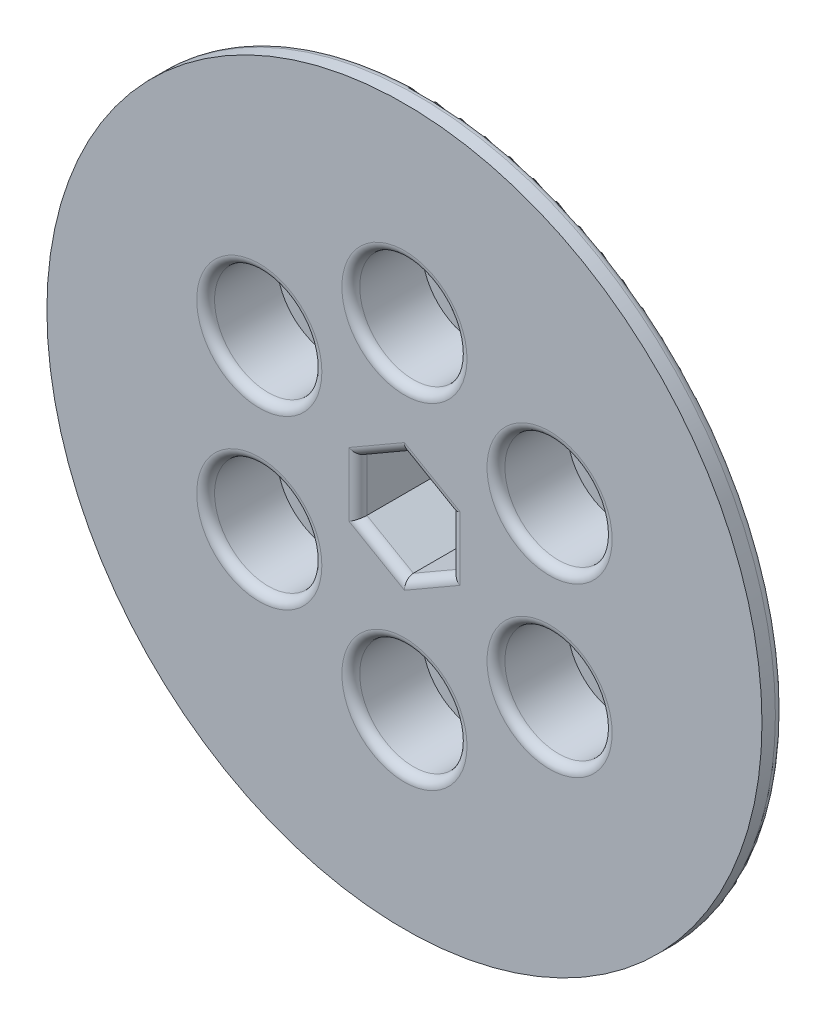
SolidWorks part; units mm, degrees
ref_plane "Front" through (0, 0, 0) normal (0, 0, 1) x (1, 0, 0)
ref_plane "Top" through (0, 0, 0) normal (0, 1, 0) x (1, 0, 0)
ref_plane "Right" through (0, 0, 0) normal (1, 0, 0) x (0, 0, -1)
sketch "Sketch1" plane through (0, 0, 0) normal (0, 0, 1) x (1, 0, 0)
  circle A0 centre (0, 0) radius 31.75
  dimension "D1" = 63.5
extrude "Boss-Extrude1" add sketch "Sketch1" along normal blind 12.7
sketch "Sketch2" plane through (0, 0, 12.7) normal (0, 0, 1) x (1, 0, 0)
  circle A1 centre (0, 0) radius 50.8
  circle A2 centre (0, 0) radius 31.75 construction
  dimension "D1" = 19.05
extrude "Boss-Extrude2" add sketch "Sketch2" along normal blind 3.175
sketch "Sketch3" plane through (0, 0, 0) normal (0, 0, -1) x (-1, 0, 0)
  line L0 (0, 0) -> (0, 23.8125) construction
  line L2 (0, 7.6256) -> (-6.604, 3.8128)
  line L3 (-6.604, 3.8128) -> (-6.604, -3.8128)
  line L4 (-6.604, -3.8128) -> (0, -7.6256)
  line L5 (0, -7.6256) -> (6.604, -3.8128)
  line L6 (6.604, -3.8128) -> (6.604, 3.8128)
  line L7 (6.604, 3.8128) -> (0, 7.6256)
  circle A0 centre (0, 23.8125) radius 2.667
  circle A1 centre (20.6222, 11.9063) radius 2.667
  circle A2 centre (20.6222, -11.9062) radius 2.667
  circle A3 centre (0, -23.8125) radius 2.667
  circle A4 centre (-20.6222, -11.9063) radius 2.667
  circle A5 centre (-20.6222, 11.9062) radius 2.667
  circle A6 centre (0, 0) radius 6.604 construction
  point P17 (0, 0)
  dimension "D2" = 5.334
  dimension "D1" = 23.8125
  dimension "D3" = 6
extrude "r" cut sketch "Sketch3" against normal up to next
sketch "Sketch4" plane through (0, 0, 15.875) normal (0, 0, 1) x (1, 0, 0)
  circle A0 centre (-20.6222, -11.9062) radius 7.62
  circle A1 centre (-20.6222, 11.9063) radius 7.62
  circle A2 centre (0, 23.8125) radius 7.62
  circle A3 centre (20.6222, 11.9062) radius 7.62
  circle A4 centre (20.6222, -11.9063) radius 7.62
  circle A5 centre (0, -23.8125) radius 7.62
  point P15 (0, 0)
  dimension "D1" = 15.24
  dimension "D2" = 6
extrude "Cut-Extrude2" cut sketch "Sketch4" against normal blind 10.16
fillet "Fillet1" radius 1.27 13 edges at (50.8, 0, 12.7) (-13.0022, 11.9063, 15.875) (7.62, 23.8125, 15.875) (28.2422, 11.9062, 15.875) (28.2422, -11.9063, 15.875) (-13.0022, -11.9062, 15.875) (7.62, -23.8125, 15.875) (6.604, 0, 15.875) (3.302, 5.7192, 15.875) (-3.302, 5.7192, 15.875) (-6.604, 0, 15.875) (-3.302, -5.7192, 15.875) (3.302, -5.7192, 15.875)
